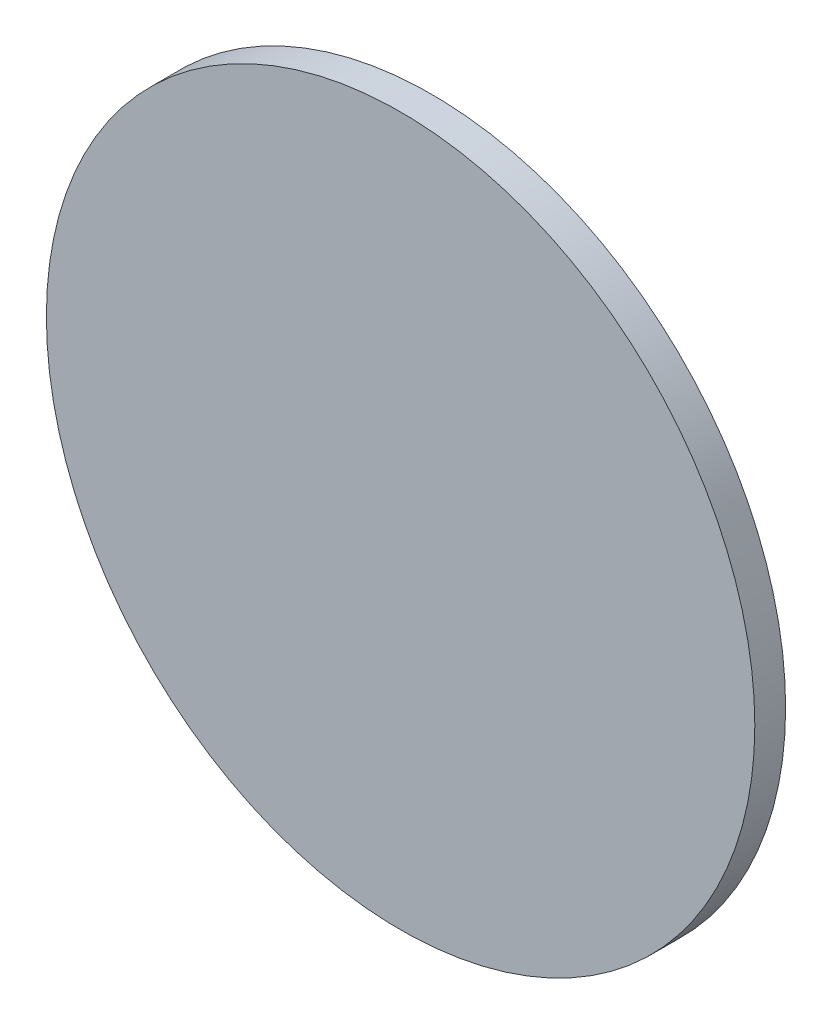
SolidWorks part; units mm, degrees
ref_plane "Front Plane" through (0, 0, 0) normal (0, 0, 1) x (1, 0, 0)
ref_plane "Top Plane" through (0, 0, 0) normal (0, 1, 0) x (1, 0, 0)
ref_plane "Right Plane" through (0, 0, 0) normal (1, 0, 0) x (0, 0, -1)
sketch "Sketch1" plane through (0, 0, 0) normal (0, 0, 1) x (1, 0, 0)
  circle A0 centre (0, 0) radius 23
  dimension "D1" = 46
extrude "Boss-Extrude1" add sketch "Sketch1" along normal blind 2
equation "\"inlet_diameter\"= 50"
equation "\"total_length\"=200"
equation "\"outlet_length\"=70"
equation "\"D2@Edge\"=\"outlet_length\""
equation "\"D1@Inlet\" = \"inlet_diameter\""
equation "\"outlet_diameter\"= 30"
equation "\"D1@Outlet\" = \"outlet_diameter\""
equation "\"side_length\"=120"
equation "\"D1@Sketch4\"=\"side_length\""
equation "\"D1@Sketch5\"=\"side_length\""
equation "\"inlet_lentgh\"=70"
equation "\"D1@Edge\"=\"inlet_lentgh\""
equation "\"D3@Edge\"=\"total_length\""
equation "\"D1@Sketch1\"=\"inlet_diameter\"-4"
